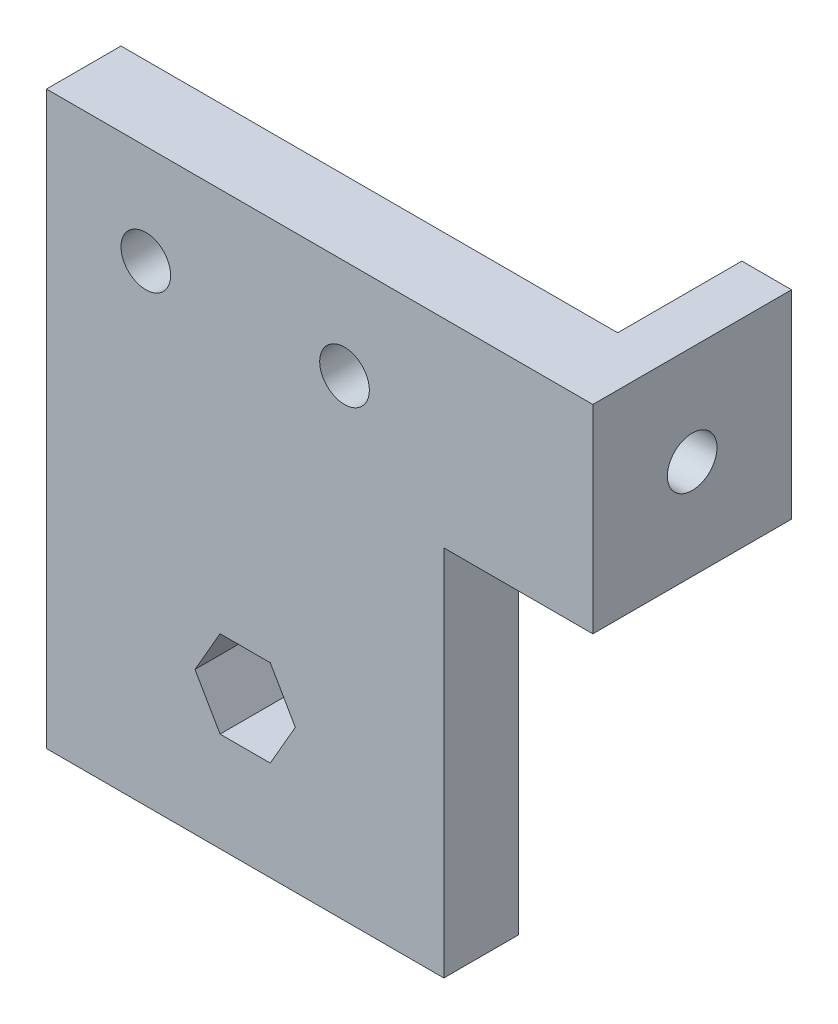
SolidWorks part; units mm, degrees
material "ABS"
ref_plane "Front Plane" through (0, 0, 0) normal (0, 0, 1) x (1, 0, 0)
ref_plane "Top Plane" through (0, 0, 0) normal (0, 1, 0) x (1, 0, 0)
ref_plane "Right Plane" through (0, 0, 0) normal (1, 0, 0) x (0, 0, -1)
sketch "Sketch2" plane through (0, 0, 0) normal (0, 0, 1) x (1, 0, 0)
  line L0 (25.4, 73.025) -> (25.4, -36.5125) construction
  line L1 (0, 0) -> (50.8, 0)
  line L2 (0, 0) -> (0, 73.025)
  line L3 (0, 73.025) -> (50.8, 73.025)
  line L4 (50.8, 0) -> (50.8, 47.625)
  line L6 (31.8158, 18.2562) -> (28.6079, 23.8125)
  line L7 (28.6079, 23.8125) -> (22.1921, 23.8125)
  line L8 (22.1921, 23.8125) -> (18.9842, 18.2562)
  line L9 (18.9842, 18.2562) -> (22.1921, 12.7)
  line L10 (22.1921, 12.7) -> (28.6079, 12.7)
  line L11 (28.6079, 12.7) -> (31.8158, 18.2562)
  line L12 (50.8, 73.025) -> (63.5, 73.025)
  line L14 (50.8, 47.625) -> (63.5, 47.625)
  line L15 (63.5, 73.025) -> (63.5, 47.625)
  circle A0 centre (12.7, 60.325) radius 3.175
  circle A1 centre (38.1, 60.325) radius 3.175
  circle A2 centre (25.4, 18.2562) radius 5.5562 construction
  dimension "D3" = 6.35
  dimension "D1" = 50.8
  dimension "D2" = 73.025
  dimension "D4" = 12.7
  dimension "D5" = 12.7
  dimension "D6" = 18.2562
  dimension "D7" = 12.7
  dimension "D8" = 25.4
extrude "Extrude1" add sketch "Sketch2" along normal blind 9.525
sketch "Sketch3" plane through (63.5, 0, 0) normal (1, 0, 0) x (0, 0, -1)
  line L1 (-9.525, 73.025) -> (15.875, 73.025)
  line L2 (-9.525, 73.025) -> (-9.525, 47.625)
  line L3 (-9.525, 47.625) -> (15.875, 47.625)
  line L4 (15.875, 73.025) -> (15.875, 47.625)
  circle A0 centre (3.175, 60.325) radius 3.175
  dimension "D3" = 6.35
  dimension "D1" = 25.4
  dimension "D2" = 25.4
  dimension "D4" = 12.7
  dimension "D5" = 12.7
extrude "Extrude2" add sketch "Sketch3" along normal blind 6.35
sketch "Sketch4" plane through (63.5, 0, 0) normal (-1, 0, 0) x (0, 0, 1)
  circle A0 centre (-3.175, 60.325) radius 5.207
  dimension "D1" = 10.414
extrude "Extrude3" cut sketch "Sketch4" along normal blind 12.7
fillet "Fillet1" radius 2 1 edges at (50.8, 60.325, 0)
